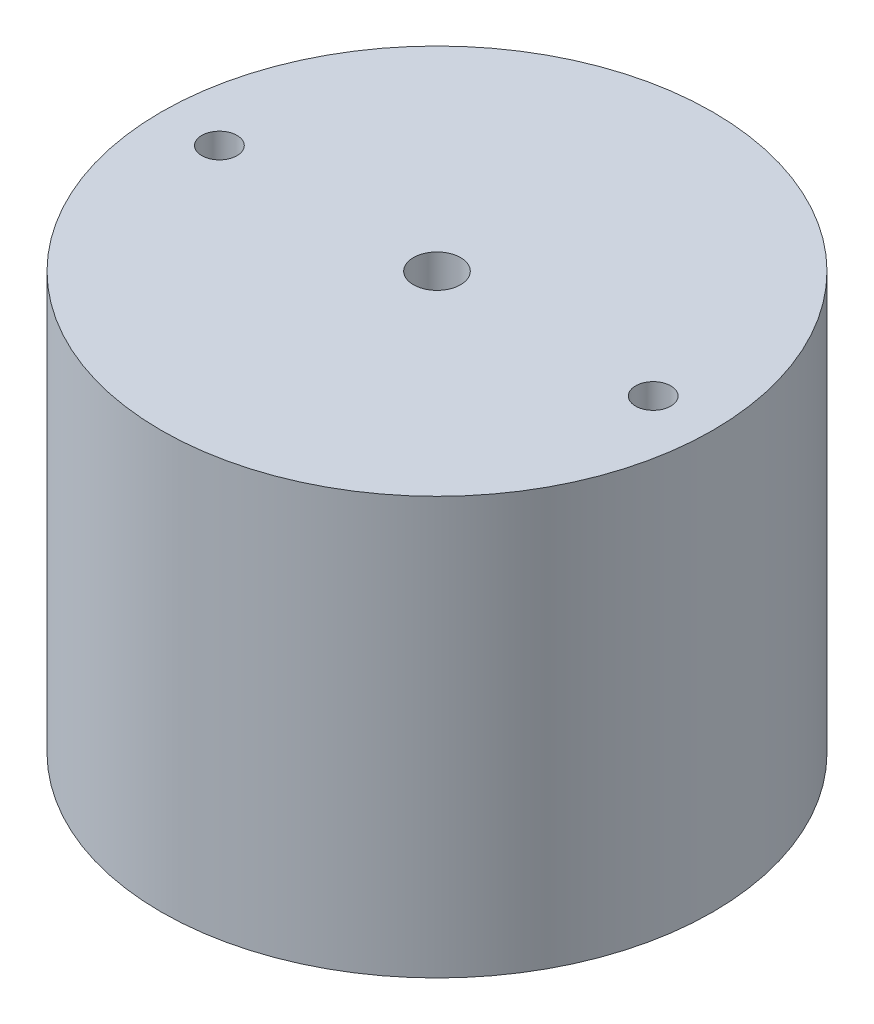
SolidWorks part; units mm, degrees
material "Monel(R) 400"
ref_plane "Front Plane" through (0, 0, 0) normal (0, 0, 1) x (1, 0, 0)
ref_plane "Top Plane" through (0, 0, 0) normal (0, 1, 0) x (1, 0, 0)
ref_plane "Right Plane" through (0, 0, 0) normal (1, 0, 0) x (0, 0, -1)
sketch "Sketch1" plane through (0, 0, 0) normal (0, 1, 0) x (1, 0, 0)
  line L0 (-59.6281, 0) -> (59.2439, 0) construction
  circle A0 centre (0, 0) radius 75.565
  circle A1 centre (0, 0) radius 6.4604
  circle A2 centre (-59.6281, 0) radius 4.826
  circle A3 centre (59.2439, 0) radius 4.826
  dimension "D1" = 118.872
  dimension "D2" = 9.652
  dimension "D3" = 9.652
  dimension "D4" = 151.13
extrude "Boss-Extrude1" add sketch "Sketch1" along normal mid plane 114.3
